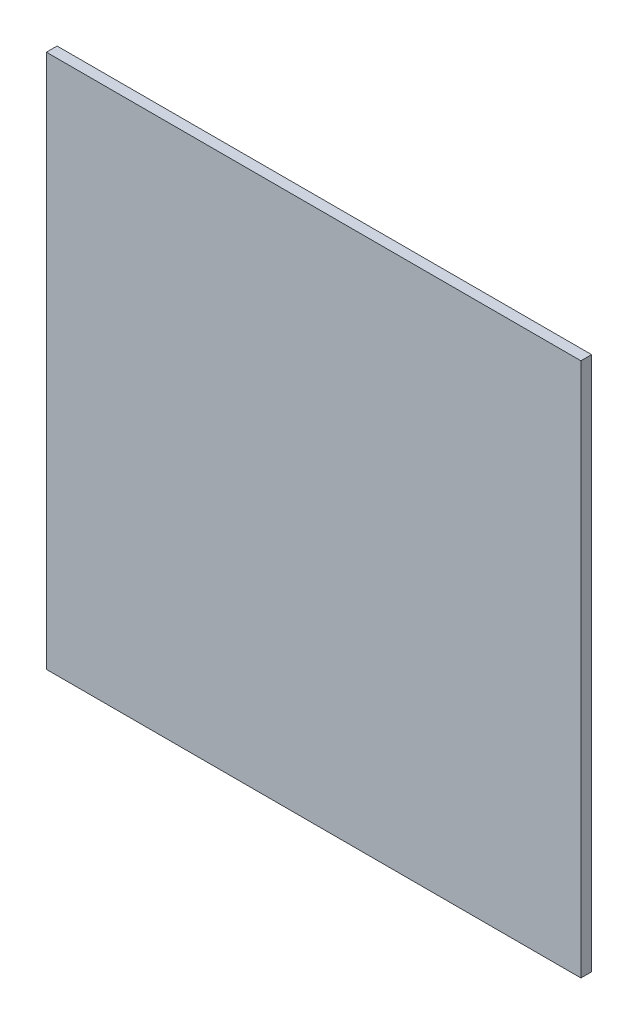
SolidWorks part; units mm, degrees
material "1.0116 (S235J2G3)"
ref_plane "Ebene vorne" through (0, 0, 0) normal (0, 0, 1) x (1, 0, 0)
ref_plane "Ebene oben" through (0, 0, 0) normal (0, 1, 0) x (1, 0, 0)
ref_plane "Ebene rechts" through (0, 0, 0) normal (1, 0, 0) x (0, 0, -1)
sketch "Skizze1" plane through (0, 0, 0) normal (0, 0, 1) x (1, 0, 0)
  line L1 (500, -500) -> (-500, -500)
  line L2 (500, -500) -> (500, 500)
  line L3 (500, 500) -> (-500, 500)
  line L4 (-500, -500) -> (-500, 500)
  line L5 (500, -500) -> (-500, 500) construction
  line L6 (500, 500) -> (-500, -500) construction
  point P0 (0, 0)
  dimension "D1" = 1000
  dimension "D2" = 1000
extrude "Aufsatz-Linear austragen1" add sketch "Skizze1" along normal blind 20
